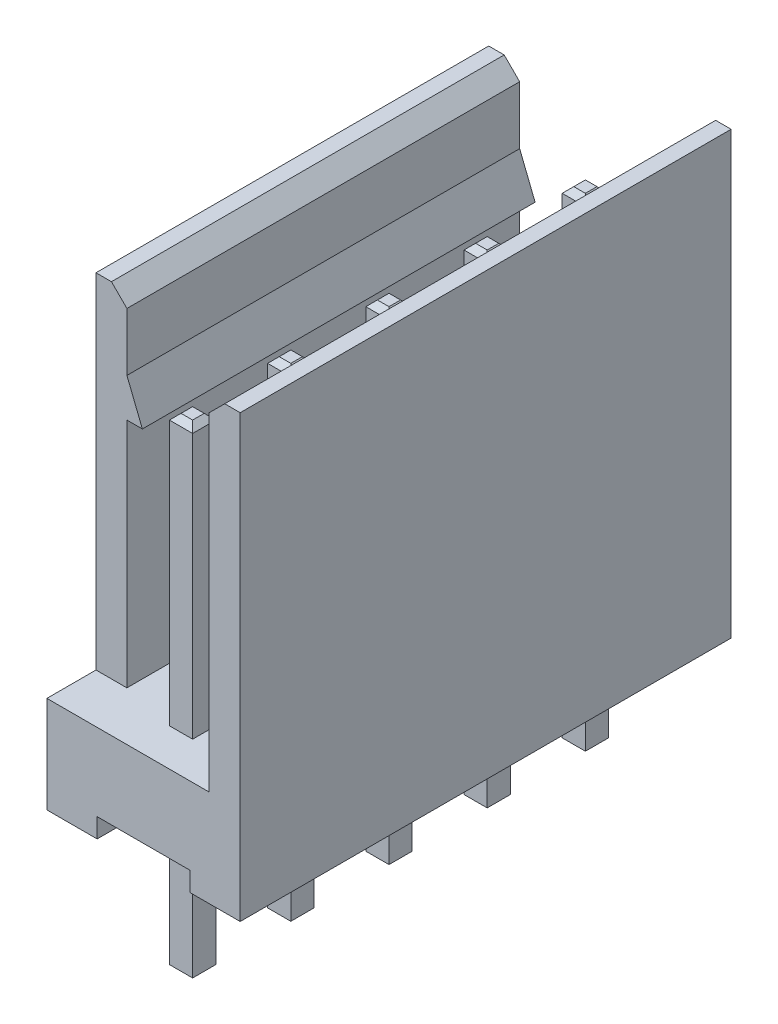
SolidWorks part; units mm, degrees
ref_plane "Plan de face" through (0, 0, 0) normal (0, 0, 1) x (1, 0, 0)
ref_plane "Plan de dessus" through (0, 0, 0) normal (0, 1, 0) x (1, 0, 0)
ref_plane "Plan de droite" through (0, 0, 0) normal (1, 0, 0) x (0, 0, -1)
sketch "Esquisse1" plane through (0, 0, 0) normal (0, 0, 1) x (1, 0, 0)
  line L0 (0, 11.4) -> (0, 0)
  line L1 (0, 0) -> (5, 0)
  line L2 (5, 0) -> (5, 11.4)
  line L3 (5, 11.4) -> (4.2, 11.4)
  line L4 (4.2, 11.4) -> (4.2, 2.5)
  line L5 (4.2, 2.5) -> (0.8, 2.5)
  line L6 (0.8, 2.5) -> (0.8, 11.4)
  line L10 (0.8, 11.4) -> (0, 11.4)
  dimension "D1" = 2.5
  dimension "D2" = 5
  dimension "D3" = 11.4
  dimension "D4" = 0.8
  dimension "D5" = 0.8
extrude "Boss.-Extru.1" add sketch "Esquisse1" along normal blind 12.7
sketch "Esquisse3" plane through (0, 11.4, 0) normal (0, 1, 0) x (1, 0, 0)
  line L0 (0.8, -12.7) -> (0.8, 0) construction
  line L1 (0, 0) -> (0.8, 0)
  line L2 (0, 0) -> (0, -1.27)
  line L3 (0, -1.27) -> (0.8, -1.27)
  line L4 (0.8, 0) -> (0.8, -1.27)
  line L6 (0, -12.7) -> (0.8, -12.7)
  line L7 (0, -12.7) -> (0, -11.43)
  line L8 (0, -11.43) -> (0.8, -11.43)
  line L9 (0.8, -12.7) -> (0.8, -11.43)
  dimension "D1" = 1.27
extrude "Enlèv. mat.-Extru.1" cut sketch "Esquisse3" against normal up to surface (8.9 mm away) up to face at (2.5, 2.5, 6.35)
sketch "Esquisse4" plane through (0, 0, 12.7) normal (0, 0, 1) x (1, 0, 0)
  line L0 (0, 0) -> (5, 0) construction
  line L1 (1.3, 0) -> (3.7, 0)
  line L2 (1.3, 0) -> (1.3, 0.5)
  line L3 (1.3, 0.5) -> (3.7, 0.5)
  line L4 (3.7, 0) -> (3.7, 0.5)
  line L5 (0, 2.5) -> (0, 0) construction
  line L6 (5, 0) -> (5, 11.4) construction
  point P8 (0, 1.25)
  dimension "D1" = 0.5
  dimension "D2" = 1.3
  dimension "D3" = 1.3
extrude "Enlèv. mat.-Extru.2" cut sketch "Esquisse4" against normal through all
sketch "Esquisse2" plane through (0, 0.5, 0) normal (0, -1, 0) x (1, 0, 0)
  line L0 (2.5, 11.43) -> (2.5, 12.7) construction
  line L1 (2.2, 11.13) -> (2.8, 11.13)
  line L2 (2.2, 11.13) -> (2.2, 11.73)
  line L3 (2.2, 11.73) -> (2.8, 11.73)
  line L4 (2.8, 11.13) -> (2.8, 11.73)
  line L5 (2.2, 11.13) -> (2.8, 11.73) construction
  line L6 (2.2, 11.73) -> (2.8, 11.13) construction
  line L7 (2.2, 0.97) -> (2.8, 0.97)
  line L8 (2.2, 0.97) -> (2.2, 1.57)
  line L9 (2.2, 1.57) -> (2.8, 1.57)
  line L10 (2.8, 0.97) -> (2.8, 1.57)
  line L11 (2.2, 0.97) -> (2.8, 1.57) construction
  line L12 (2.2, 1.57) -> (2.8, 0.97) construction
  line L13 (2.5, 11.43) -> (2.5, 8.89) construction
  line L14 (2.2, 9.19) -> (2.8, 9.19)
  line L15 (2.2, 9.19) -> (2.2, 8.59)
  line L16 (2.5, 1.27) -> (2.5, 0) construction
  line L17 (2.2, 8.59) -> (2.8, 8.59)
  line L18 (3.7, 12.7) -> (1.3, 12.7) construction
  line L19 (3.7, 0) -> (1.3, 0) construction
  line L20 (2.8, 9.19) -> (2.8, 8.59)
  line L21 (2.2, 9.19) -> (2.8, 8.59) construction
  line L22 (2.2, 8.59) -> (2.8, 9.19) construction
  line L23 (2.2, 6.65) -> (2.8, 6.65)
  line L24 (2.2, 6.65) -> (2.2, 6.05)
  line L25 (2.2, 6.05) -> (2.8, 6.05)
  line L26 (2.8, 6.65) -> (2.8, 6.05)
  line L27 (2.2, 6.65) -> (2.8, 6.05) construction
  line L28 (2.2, 6.05) -> (2.8, 6.65) construction
  line L29 (2.2, 4.11) -> (2.8, 4.11)
  line L30 (2.2, 4.11) -> (2.2, 3.51)
  line L31 (2.2, 3.51) -> (2.8, 3.51)
  line L32 (2.8, 4.11) -> (2.8, 3.51)
  line L33 (2.2, 4.11) -> (2.8, 3.51) construction
  line L34 (2.2, 3.51) -> (2.8, 4.11) construction
  line L35 (2.5, 8.89) -> (2.5, 6.35) construction
  line L36 (2.5, 6.35) -> (2.5, 3.81) construction
  line L37 (2.5, 3.81) -> (2.5, 1.27) construction
  point P0 (2.5, 11.43)
  point P5 (2.5, 1.27)
  point P12 (2.5, 6.35)
  point P16 (2.5, 8.89)
  point P28 (2.5, 3.81)
  dimension "D1" = 0.6
  dimension "D2" = 2.54
extrude "Boss.-Extru.2" add sketch "Esquisse2" along normal blind 3.5 and the other way blind 9
sketch "Esquisse5" plane through (0, 0, 11.43) normal (0, 0, 1) x (1, 0, 0)
  line L0 (0.8, 9.5) -> (1.2, 8.5)
  line L1 (0.8, 2.5) -> (0.8, 11.4) construction
  line L2 (1.2, 8.5) -> (0.8, 8.5)
  line L3 (0.8, 8.5) -> (0.8, 9.5)
  line L4 (2.8, 9.5) -> (2.2, 9.5) construction
  dimension "D1" = 1
  dimension "D2" = 0.4
extrude "Boss.-Extru.3" add sketch "Esquisse5" against normal up to surface (10.16 mm away) up to face at (0.4, 6.95, 1.27)
chamfer "Chanfrein4" distance 0.15 angle 45 40 edges at (2.5, -3, 11.13) (2.2, -3, 11.43) (2.5, -3, 11.73) (2.8, -3, 11.43) (2.5, -3, 0.97) (2.2, -3, 1.27) (2.5, -3, 1.57) (2.8, -3, 1.27) (2.5, 9.5, 11.73) (2.2, 9.5, 11.43) (2.5, 9.5, 11.13) (2.8, 9.5, 11.43) (2.5, 9.5, 1.57) (2.2, 9.5, 1.27) (2.5, 9.5, 0.97) (2.8, 9.5, 1.27) (2.5, -3, 3.51) (2.2, -3, 3.81) (2.5, -3, 4.11) (2.8, -3, 3.81) (2.5, -3, 6.05) (2.2, -3, 6.35) (2.5, -3, 6.65) (2.8, -3, 6.35) (2.5, -3, 8.59) (2.2, -3, 8.89) (2.5, -3, 9.19) (2.8, -3, 8.89) (2.5, 9.5, 4.11) (2.2, 9.5, 3.81) (2.5, 9.5, 3.51) (2.8, 9.5, 3.81) (2.5, 9.5, 6.65) (2.2, 9.5, 6.35) (2.5, 9.5, 6.05) (2.8, 9.5, 6.35) (2.5, 9.5, 9.19) (2.2, 9.5, 8.89) (2.5, 9.5, 8.59) (2.8, 9.5, 8.89)
chamfer "Chanfrein5" distance 0.4 angle 45 2 edges at (4.2, 11.4, 6.35) (0.8, 11.4, 6.35)
